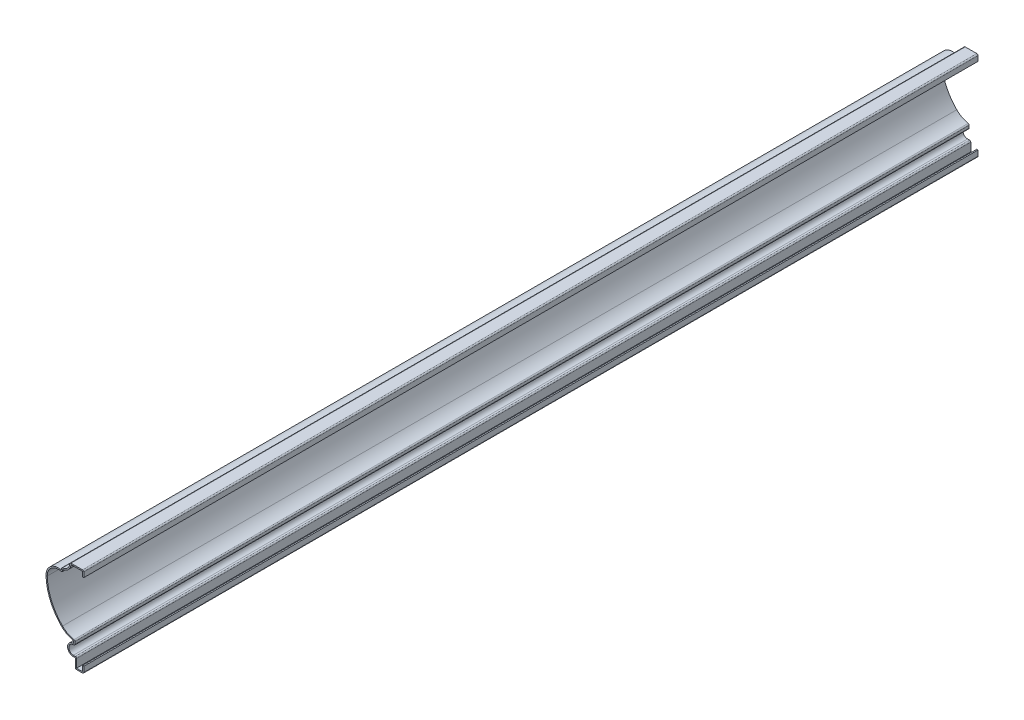
SolidWorks part; units mm, degrees
ref_plane "Front Plane" through (0, 0, 0) normal (0, 0, 1) x (1, 0, 0)
ref_plane "Top Plane" through (0, 0, 0) normal (0, 1, 0) x (1, 0, 0)
ref_plane "Right Plane" through (0, 0, 0) normal (1, 0, 0) x (0, 0, -1)
sketch "Sketch3" plane through (0, 0, 0) normal (0, 0, 1) x (1, 0, 0)
  line L0 (0, 0) -> (0, 78.9781) construction
  line L1 (0, 78.9781) -> (0, 85.3281)
  line L2 (0, 85.3281) -> (-14.2875, 85.3281)
  line L3 (-23.0187, 76.5969) -> (-23.0187, 74.2024)
  line L4 (-10.3188, 17.4493) -> (-10.3188, 15.068)
  line L5 (-8.7313, 3.175) -> (-8.7312, -6.7469)
  line L6 (-8.7312, -6.7469) -> (0, -6.7469)
  line L7 (0, -6.7469) -> (0, 0)
  line L8 (0, 63.0206) -> (16.2572, 63.0206) construction
  line L9 (16.2572, 63.0206) -> (-22.7508, 24.0126) construction
  line L10 (-10.7156, 3.175) -> (-8.7313, 3.175)
  arc A0 (-14.2875, 85.3281) -> (-23.0187, 76.5969) centre (-23.0187, 85.3281) cw
  arc A1 (-23.0187, 74.2024) -> (-38.8894, 61.5722) centre (-26.1937, 61.9057) ccw
  arc A2 (-38.8894, 61.5722) -> (-22.7508, 24.0126) centre (16.2572, 63.0206) ccw
  arc A3 (-22.7508, 24.0126) -> (-10.3188, 17.4493) centre (-5.9128, 40.8506) ccw
  arc A4 (-10.3188, 15.068) -> (-10.7156, 3.175) centre (-10.7156, 9.1281) ccw
  point P17 (0, 0)
  point P21 (-10.3187, -7.6987)
  point P22 (-22.4086, 74.2024)
  point P23 (-36.1324, 62.3229)
  point P24 (-42.4212, 63.415)
  point P25 (12.7444, 63.415)
  point P26 (-29.7212, 63.415)
  point P28 (-42.4212, 63.415)
  dimension "D2" = 12.7
  dimension "D3" = 55.1656
  dimension "D4" = 23.8125
  dimension "D6" = 16.6687
  dimension "D11" = 5.9531
  dimension "D17" = 8.7312
  dimension "D1" = 6.35
  dimension "D5" = 45
  dimension "D7" = 2.3813
  dimension "D8" = 9.9219
  dimension "D9" = 8.7312
  dimension "D10" = 10.3187
  dimension "D12" = 6.7469
  dimension "D13" = 56.7531
  dimension "D14" = 92.075
  dimension "D15" = 8.7312
  dimension "D16" = 14.2875
  dimension "D18" = 38.8937
extrude "Extrude-Thin1" add sketch "Sketch3" against normal blind 920.75 thin thin type one direction reverse wall 1.27
fillet "Fillet1" radius 1.27 9 edges at (0, -6.7469, -460.375) (-8.7312, -6.7469, -460.375) (-7.4613, 4.445, -460.375) (-9.0488, 13.5046, -460.375) (-9.0488, 18.5273, -460.375) (-21.7487, 72.4359, -460.375) (-23.0187, 76.5969, -460.375) (-14.2875, 85.3281, -460.375) (0, 85.3281, -460.375)
